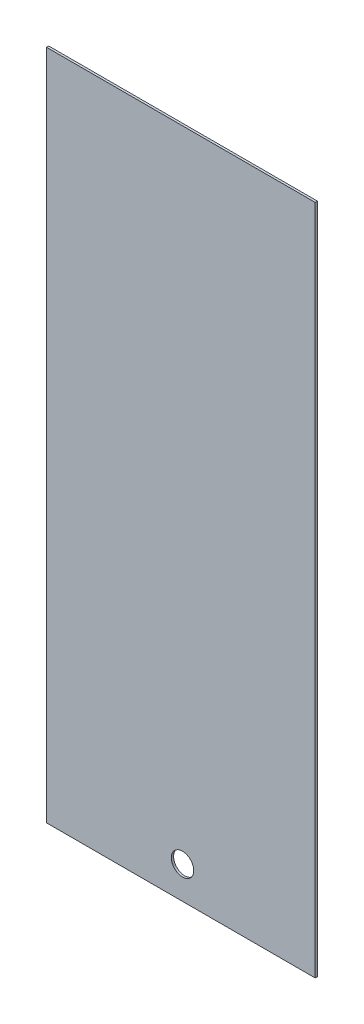
SolidWorks part; units mm, degrees
material "PVC Rigid"
ref_plane "Front Plane" through (0, 0, 0) normal (0, 0, 1) x (1, 0, 0)
ref_plane "Top Plane" through (0, 0, 0) normal (0, 1, 0) x (1, 0, 0)
ref_plane "Right Plane" through (0, 0, 0) normal (1, 0, 0) x (0, 0, -1)
sketch "Sketch1" plane through (0, 0, 0) normal (0, 0, 1) x (1, 0, 0)
  line L1 (-177.4684, 180.2538) -> (127.3316, 180.2538)
  line L2 (-177.4684, 180.2538) -> (-177.4684, -581.7462)
  line L3 (-177.4684, -581.7462) -> (127.3316, -581.7462)
  line L4 (127.3316, 180.2538) -> (127.3316, -581.7462)
  dimension "D1" = 762
  dimension "D2" = 304.8
extrude "Boss-Extrude1" add sketch "Sketch1" along normal blind 2.54
sketch "Sketch2" plane through (0, 0, 2.54) normal (0, 0, 1) x (1, 0, 0)
  circle A0 centre (-23.1932, -545.1629) radius 12.7
  dimension "D1" = 25.4
extrude "Cut-Extrude1" cut sketch "Sketch2" against normal through all
